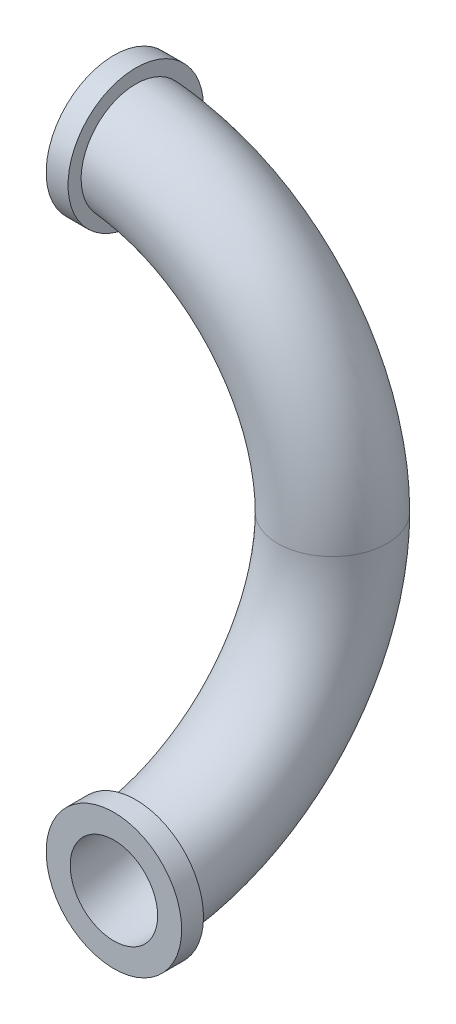
SolidWorks part; units mm, degrees
ref_plane "Ön Düzlem" through (0, 0, 0) normal (0, 0, 1) x (1, 0, 0)
ref_plane "Üst Düzlem" through (0, 0, 0) normal (0, 1, 0) x (1, 0, 0)
ref_plane "Sağ Düzlem" through (0, 0, 0) normal (1, 0, 0) x (0, 0, -1)
sketch3d "3B Çizim1"
  arc A0 (0, 0, 0) -> (-1, 1, 0) centre (-1, 0, 0) ccw
  arc A1 (0, 0, 0) -> (0, -1, 1) centre (0, 0, 1) cw
  point P0 (-1, 0, 0)
  point P3 (-1, 0, 1)
  point P6 (0, 0, 1)
  point P10 (-1, 0, 1)
sketch "Çizim2" plane through (0, 0, 0) normal (1, 0, 0) x (0, 0, -1)
  line L0 (-1, -1) -> (-0.9, -1)
sketch "Çizim3" plane through (0, 0, 0) normal (0, 0, 1) x (1, 0, 0)
  line L0 (-1, 1) -> (-0.9, 1)
ref_plane "Düzlem1" through (0, 0, 1) normal (0, 0, 1) x (1, 0, 0)
sketch "Çizim4" plane through (0, 0, 1) normal (0, 0, 1) x (1, 0, 0)
  circle A0 centre (0, -1) radius 0.2
sketch "Çizim5" plane through (0, 0, 1) normal (0, 0, 1) x (1, 0, 0)
  circle A0 centre (0, -1) radius 0.21
ref_plane "Düzlem2" through (-1, 0, 0) normal (1, 0, 0) x (0, 0, -1)
sketch "Çizim6" plane through (-1, 0, 0) normal (1, 0, 0) x (0, 0, -1)
  circle A0 centre (0, 1) radius 0.21
sweep "Süpür-İnce1" add profiles "Çizim4" path "3B Çizim1" parameters "D1"=0.05
sweep "Süpür-İnce2" add profiles "Çizim5" path "Çizim2" parameters "D1"=0.1
sweep "Süpür-İnce3" add profiles "Çizim6" path "Çizim3" parameters "D1"=0.1
